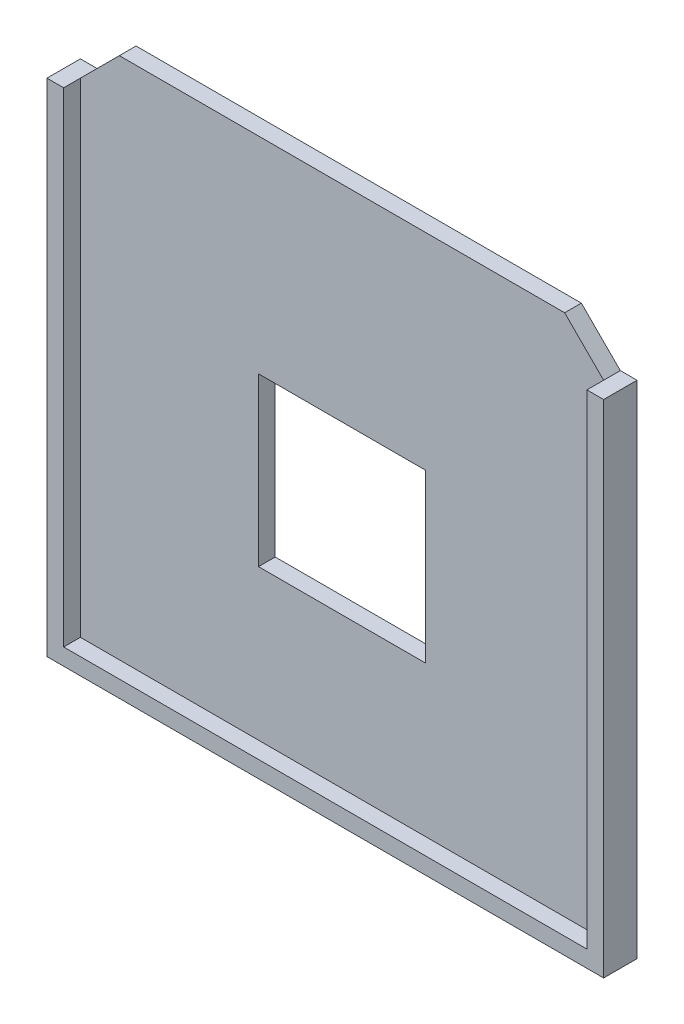
SolidWorks part; units mm, degrees
ref_plane "Alzado" through (0, 0, 0) normal (0, 0, 1) x (1, 0, 0)
ref_plane "Planta" through (0, 0, 0) normal (0, 1, 0) x (1, 0, 0)
ref_plane "Vista lateral" through (0, 0, 0) normal (1, 0, 0) x (0, 0, -1)
sketch "Croquis1" plane through (0, 0, 0) normal (0, 0, 1) x (1, 0, 0)
  line L0 (-50, 45) -> (-47, 45)
  line L1 (-50, -45) -> (50, -45)
  line L2 (-50, -45) -> (-50, 45)
  line L4 (50, -45) -> (50, 45)
  line L5 (-50, -45) -> (50, 45) construction
  line L6 (-50, 45) -> (50, -45) construction
  line L7 (-47, 45) -> (-40, 52)
  line L8 (-40, 52) -> (40, 52)
  line L9 (40, 52) -> (47, 45)
  line L10 (47, 45) -> (50, 45)
  point P0 (0, 0)
  dimension "D1" = 100
  dimension "D2" = 90
  dimension "D3" = 3
  dimension "D4" = 135
  dimension "D5" = 135
  dimension "D6" = 7
extrude "Saliente-Extruir1" add sketch "Croquis1" along normal blind 3
sketch "Croquis3" plane through (0, 0, 3) normal (0, 0, 1) x (1, 0, 0)
  line L1 (-15, -15) -> (15, -15)
  line L2 (-15, -15) -> (-15, 15)
  line L3 (-15, 15) -> (15, 15)
  line L4 (15, -15) -> (15, 15)
  line L5 (-15, -15) -> (15, 15) construction
  line L6 (-15, 15) -> (15, -15) construction
  point P1 (0, 0)
  dimension "D1" = 30
  dimension "D2" = 30
extrude "Cortar-Extruir1" cut sketch "Croquis3" against normal blind 3
sketch "Croquis4" plane through (0, 0, 3) normal (0, 0, 1) x (1, 0, 0)
  line L0 (-50, 45) -> (-47, 45)
  line L1 (-47, 45) -> (-47, -42)
  line L2 (-47, -42) -> (47, -42)
  line L3 (47, -42) -> (47, 45)
  line L4 (47, 45) -> (50, 45)
  line L5 (50, 45) -> (50, -45)
  line L6 (50, -45) -> (-50, -45)
  line L7 (-50, -45) -> (-50, 45)
  dimension "D1" = 3
extrude "Saliente-Extruir2" add sketch "Croquis4" along normal blind 3
